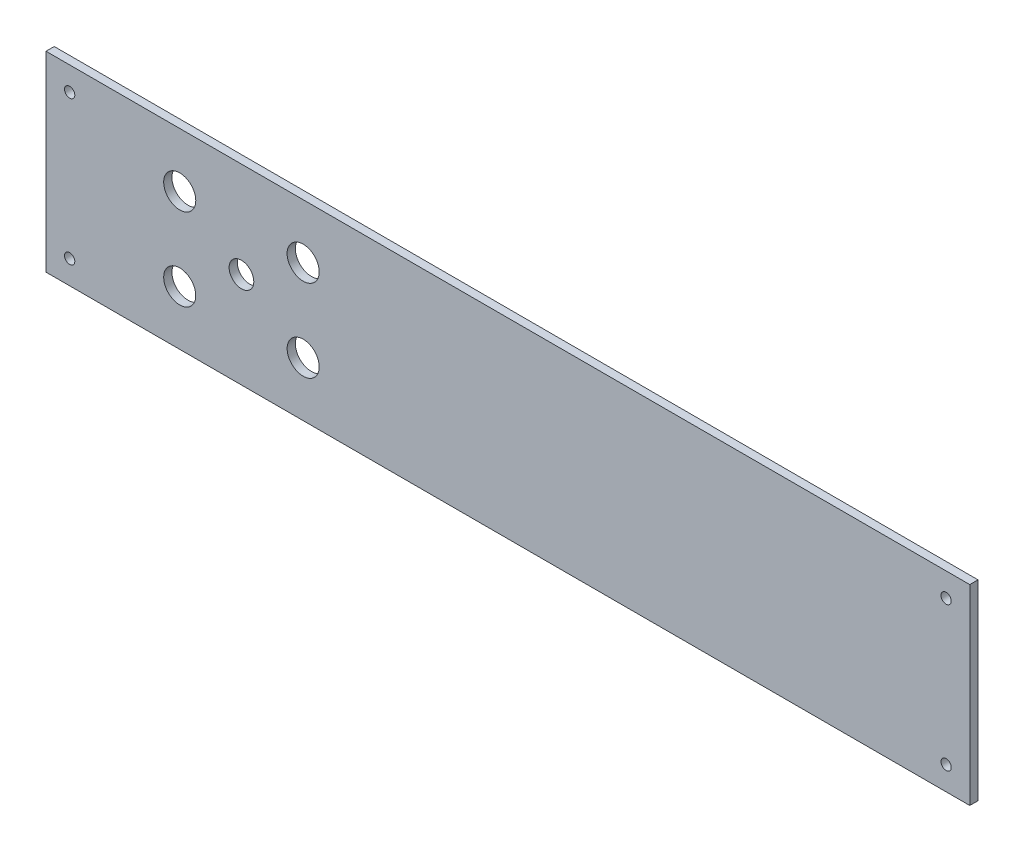
SolidWorks part; units mm, degrees
material "PERSPEX® GS in fogli"
ref_plane "Piano frontale" through (0, 0, 0) normal (0, 0, 1) x (1, 0, 0)
ref_plane "Piano superiore" through (0, 0, 0) normal (0, 1, 0) x (1, 0, 0)
ref_plane "Piano destro" through (0, 0, 0) normal (1, 0, 0) x (0, 0, -1)
sketch "Schizzo1" plane through (0, 0, 0) normal (0, 0, 1) x (1, 0, 0)
  line L0 (-449, 46.5) -> (0, 46.5) construction
  line L1 (0, 0) -> (-449, 0)
  line L2 (0, 0) -> (0, 93)
  line L3 (0, 93) -> (-449, 93)
  line L4 (-449, 0) -> (-449, 93)
  line L5 (-224.5, 93) -> (-224.5, 0) construction
  line L8 (-354, 66.5) -> (-354, 26.5) construction
  circle A0 centre (-384, 26.5) radius 7.8
  circle A1 centre (-437.5, 81.5) radius 2.5
  circle A2 centre (-11.5, 81.5) radius 2.5
  circle A3 centre (-11.5, 11.5) radius 2.5
  circle A4 centre (-437.5, 11.5) radius 2.5
  circle A5 centre (-324, 26.5) radius 7.8
  circle A6 centre (-324, 66.5) radius 7.8
  circle A8 centre (-384, 66.5) radius 7.8
  circle A16 centre (-354, 46.5) radius 6
  dimension "D3" = 11.5
  dimension "D2" = 11.5
  dimension "D5" = 65
  dimension "D12" = 15.6
  dimension "D17" = 12
  dimension "D4" = 5
  dimension "D1" = 449
  dimension "314" = 93
  dimension "D7" = 30
  dimension "D15" = 95
extrude "Estrusione-Estrusione1" add sketch "Schizzo1" along normal blind 4
